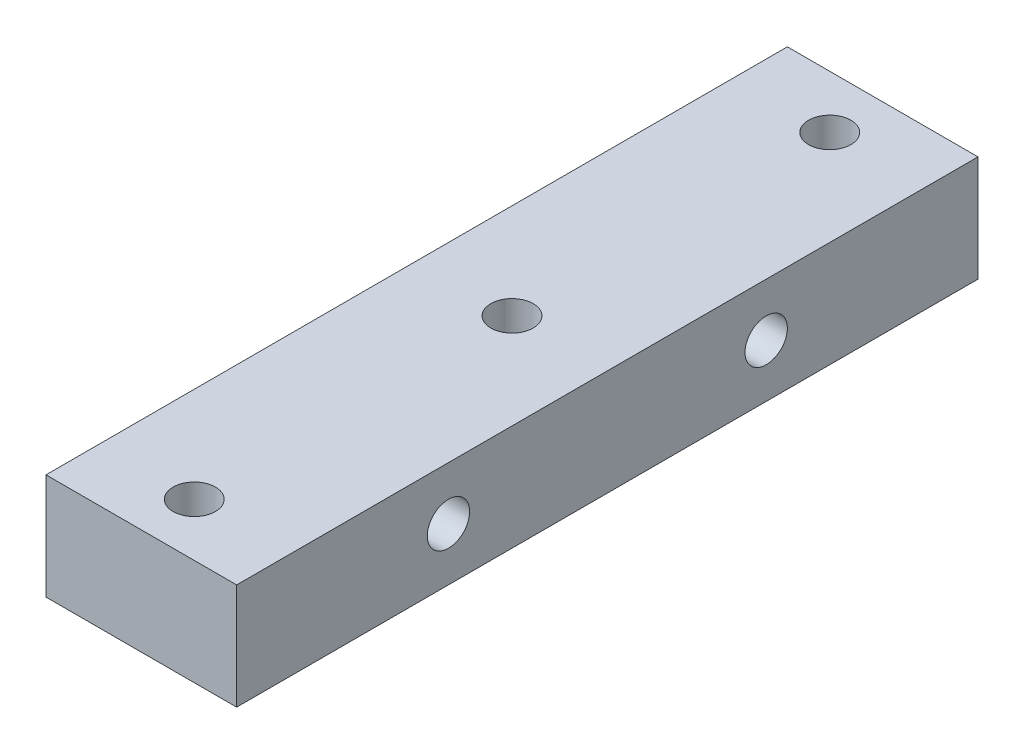
SolidWorks part; units mm, degrees
material "6061-T6 (SS)"
ref_plane "前视基准面" through (0, 0, 0) normal (0, 0, 1) x (1, 0, 0)
ref_plane "上视基准面" through (0, 0, 0) normal (0, 1, 0) x (1, 0, 0)
ref_plane "右视基准面" through (0, 0, 0) normal (1, 0, 0) x (0, 0, -1)
sketch "草图1" plane through (0, 0, 0) normal (0, 0, 1) x (1, 0, 0)
  line L1 (-9, 5) -> (9, 5)
  line L2 (-9, 5) -> (-9, -5)
  line L3 (-9, -5) -> (9, -5)
  line L4 (9, 5) -> (9, -5)
  line L5 (0, -5) -> (0, 5) construction
  line L6 (-9, 0) -> (9, 0) construction
  point P0 (0, 0)
  dimension "D1" = 18
  dimension "D2" = 10
extrude "凸台-拉伸1" add sketch "草图1" along normal blind 70
sketch "草图2" plane through (0, 5, 0) normal (0, 1, 0) x (1, 0, 0)
  line L0 (-9, -35) -> (-50009, -35) construction
  line L1 (-9, -70) -> (-9, 0) construction
  line L2 (0, 0) -> (0, -50000) construction
  line L3 (9, 0) -> (-9, 0) construction
  circle A0 centre (0, -5) radius 2
  circle A1 centre (0, -35) radius 2
  circle A2 centre (0, -65) radius 2
  point P4 (-9, -35)
  point P9 (0, 0)
  dimension "D1" = 4
  dimension "D2" = 30
extrude "切除-拉伸1" cut sketch "草图2" against normal through all
cosmetic thread "装饰螺纹线1" parameters "D2"=5
cosmetic thread "装饰螺纹线2" parameters "D2"=5
cosmetic thread "装饰螺纹线3" parameters "D2"=5
sketch "草图3" plane through (9, 0, 0) normal (1, 0, 0) x (0, 0, -1)
  line L0 (-35, 5) -> (-35, -49995) construction
  line L1 (-70, 5) -> (0, 5) construction
  line L2 (-68, 0) -> (49932, 0) construction
  line L3 (-70, -5) -> (-70, 5) construction
  circle A0 centre (-50, 0) radius 2
  circle A1 centre (-20, 0) radius 2
  point P4 (-35, 5)
  point P9 (-70, 0)
  dimension "D1" = 4
  dimension "D2" = 15
extrude "切除-拉伸2" cut sketch "草图3" against normal through all
cosmetic thread "装饰螺纹线4" parameters "D2"=5
cosmetic thread "装饰螺纹线5" parameters "D2"=5
